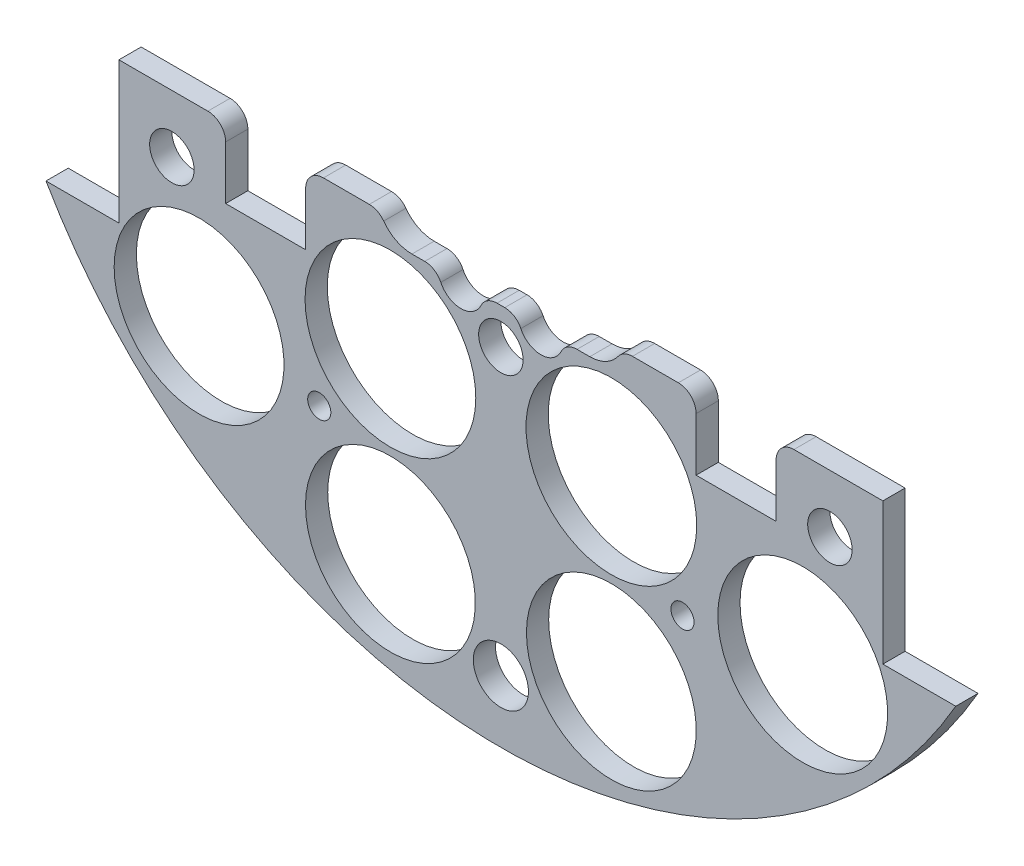
SolidWorks part; units mm, degrees
ref_plane "Front Plane" through (0, 0, 0) normal (0, 0, 1) x (1, 0, 0)
ref_plane "Top Plane" through (0, 0, 0) normal (0, 1, 0) x (1, 0, 0)
ref_plane "Right Plane" through (0, 0, 0) normal (1, 0, 0) x (0, 0, -1)
sketch "Sketch1" plane through (0, 0, 0) normal (0, 0, 1) x (1, 0, 0)
  line L0 (0, 0) -> (-82.1241, 0) construction
  line L1 (0, 0) -> (0, 95.6219) construction
  line L3 (-64.9644, 37.338) -> (-54.5504, 37.338)
  line L5 (-64.9644, -37.338) -> (-54.5504, -37.338)
  line L6 (-54.5504, 37.338) -> (-54.5504, -37.338)
  line L7 (64.9644, -37.338) -> (54.5504, -37.338)
  line L8 (64.9644, 37.338) -> (54.5504, 37.338)
  line L9 (54.5504, 37.338) -> (54.5504, -37.338)
  arc A0 (-64.9644, -37.338) -> (64.9644, -37.338) centre (0, 0) ccw
  circle A1 centre (-46.482, 11.049) radius 1.651
  circle A2 centre (-21.0833, 10.795) radius 1.651
  circle A3 centre (-21.0833, -10.795) radius 1.651
  circle A4 centre (-46.482, -11.049) radius 1.651
  circle A5 centre (46.482, -11.049) radius 1.651
  circle A6 centre (21.0833, -10.795) radius 1.651
  circle A7 centre (21.0833, 10.795) radius 1.651
  circle A8 centre (46.482, 11.049) radius 1.651
  arc A9 (64.9644, 37.338) -> (-64.9644, 37.338) centre (0, 0) ccw
  dimension "D2" = 3.302
  dimension "D3" = 3.302
  dimension "D4" = 25.4
  dimension "D5" = 10.795
  dimension "D10" = 46.482
  dimension "D6" = 74.676
  dimension "D7" = 10.414
  dimension "D8" = 74.93
  dimension "D9" = 74.93
  dimension "D11" = 37.338
extrude "Boss-Extrude2" add sketch "Sketch1" along normal blind 3.175
sketch "Sketch2" plane through (0, 0, 3.175) normal (0, 0, 1) x (1, 0, 0)
  line L0 (0, 68.58) -> (0, 55.88) construction
  line L1 (-9.525, 68.58) -> (9.525, 68.58)
  line L2 (-9.525, 68.58) -> (-9.525, 55.88)
  line L3 (-9.525, 55.88) -> (9.525, 55.88)
  line L4 (9.525, 68.58) -> (9.525, 55.88)
  line L5 (-9.525, 62.23) -> (9.525, 62.23) construction
  arc A0 (64.9644, 37.338) -> (-64.9644, 37.338) centre (0, 0) ccw construction
  circle A1 centre (-21.0833, 10.795) radius 1.651 construction
  circle A2 centre (21.0833, 10.795) radius 1.651 construction
  circle A3 centre (-6.731, 62.23) radius 1.143
  circle A4 centre (6.731, 62.23) radius 1.143
  dimension "D4" = 2.286
  dimension "D5" = 0
  dimension "D6" = 6.731
  dimension "D1" = 19.05
  dimension "D2" = 12.7
  dimension "D3" = 55.88
extrude "Cut-Extrude1" cut sketch "Sketch2" against normal through all contours A3 | A4
sketch "Sketch3" plane through (0, 0, 0) normal (0, 0, -1) x (-1, 0, 0)
  line L0 (0, 0) -> (0, -116.2908) construction
  line L1 (0, 0) -> (-153.8039, 0) construction
  line L2 (0, 0) -> (15.2681, -56.9814) construction
  line L3 (0, 0) -> (15.2302, -26.3795) construction
  circle A0 centre (-15.7776, -58.8828) radius 12.1285
  circle A3 centre (15.7776, -58.8828) radius 12.1285
  circle A4 centre (-43.1052, -43.1052) radius 12.1285
  circle A8 centre (-43.1052, 43.1052) radius 12.1285
  circle A11 centre (43.1052, 43.1052) radius 12.1285
  circle A14 centre (43.1052, -43.1052) radius 12.1285
  circle A33 centre (58.8828, -15.7776) radius 12.1285 [skipped]
  circle A34 centre (58.8828, 15.7776) radius 12.1285 [skipped]
  circle A35 centre (-58.8828, 15.7776) radius 12.1285 [skipped]
  circle A36 centre (-58.8828, -15.7776) radius 12.1285 [skipped]
  circle A37 centre (-15.7776, 58.8828) radius 12.1285 [skipped]
  circle A38 centre (15.7776, 58.8828) radius 12.1285 [skipped]
  point P36 (0, 0)
  point P53 (0, 0)
  point P55 (0, 0)
  dimension "D3" = 0
  dimension "D4" = 15
  dimension "D5" = 24.257
  dimension "D7" = 12
  dimension "D9" = 30
extrude "Cut-Extrude2" cut sketch "Sketch3" against normal through all
sketch "Sketch4" plane through (0, 0, 0) normal (0, 0, -1) x (-1, 0, 0)
  line L1 (-15.7702, 56.3138) -> (12.7925, 56.3138)
  line L2 (-15.7702, 56.3138) -> (-15.7702, 67.9913)
  line L3 (-15.7702, 67.9913) -> (12.7925, 67.9913)
  line L4 (12.7925, 56.3138) -> (12.7925, 67.9913)
extrude "Boss-Extrude3" add sketch "Sketch4" against normal up to surface (3.175 mm away) up to face at (-55.2337, -43.1052, 3.175)
sketch "Sketch5" plane through (0, 0, 0) normal (0, 0, -1) x (-1, 0, 0)
  line L1 (-85.044, -17.145) -> (131.6774, -17.145)
  line L2 (-85.044, -17.145) -> (-85.044, 113.4242)
  line L3 (-85.044, 113.4242) -> (131.6774, 113.4242)
  line L4 (131.6774, -17.145) -> (131.6774, 113.4242)
  circle A0 centre (-21.0833, -10.795) radius 1.651 construction
  dimension "D1" = 6.35
extrude "Cut-Extrude4" cut sketch "Sketch5" against normal through all contours L2 L3 L4 L1
extrude "Cut-Extrude5" cut sketch "Sketch6" against normal through all both and the other way through all
sketch "Sketch6" plane through (31.3134, 132.614, -3.175) normal (0, 0, -1) x (0, 1, 0)
  line L0 (-132.614, -31.3134) -> (-132.614, 57.8454) construction
  line L1 (-132.614, -31.3134) -> (-222.516, -31.3134) construction
  circle A0 centre (-158.014, 14.4066) radius 3.175
  circle A1 centre (-173.254, -31.3134) radius 3.175
  circle A3 centre (-158.014, -77.0334) radius 3.175
  circle A4 centre (-107.214, -77.0334) radius 3.175
  circle A5 centre (-91.974, -31.3134) radius 3.175
  circle A6 centre (-107.214, 14.4066) radius 3.175
extrude "Cut-Extrude7" cut sketch "Sketch8" against normal blind 29.21
sketch "Sketch8" plane through (31.3134, 132.559, 0) normal (0, 0, -1) x (0, 1, 0)
  line L0 (-132.559, -31.3134) -> (6.1626, -31.3134) construction
  line L2 (-132.559, -31.3134) -> (-132.559, -122.6589) construction
  circle A0 centre (-190.979, 2.9766) radius 1.651
  circle A2 centre (-154.784, -31.3134) radius 1.651
  circle A3 centre (-190.979, -65.6034) radius 1.651
  circle A4 centre (-110.334, -31.3134) radius 1.651
  circle A5 centre (-74.139, -65.6034) radius 1.651
  circle A6 centre (-74.139, 2.9766) radius 1.651
sketch "Sketch11" plane through (0, 0, 0) normal (0, 0, -1) x (-1, 0, 0)
  line L0 (-54.5504, -17.145) -> (54.5504, -17.145) construction
  circle A0 centre (0, -66.045) radius 3.937
  point P4 (0, -17.145)
  dimension "D1" = 7.874
  dimension "D2" = 48.9
extrude "Cut-Extrude11" cut sketch "Sketch11" against normal through all
sketch "Sketch12" plane through (0, 0, 0) normal (0, 0, -1) x (-1, 0, 0)
  line L0 (-54.5504, -17.145) -> (54.5504, -17.145) construction
  line L1 (-39.3104, -17.145) -> (-27.8804, -17.145)
  line L2 (-39.3104, -17.145) -> (-39.3104, -27.305)
  line L3 (-39.3104, -27.305) -> (-27.8804, -27.305)
  line L4 (-27.8804, -17.145) -> (-27.8804, -27.305)
  line L5 (-54.5504, -37.338) -> (-54.5504, -17.145) construction
  line L6 (27.8804, -17.145) -> (39.3104, -17.145)
  line L7 (27.8804, -17.145) -> (27.8804, -27.305)
  line L8 (27.8804, -27.305) -> (39.3104, -27.305)
  line L9 (39.3104, -17.145) -> (39.3104, -27.305)
  line L10 (0, -10.2409) -> (0, -88.0539) construction
  dimension "D1" = 15.24
  dimension "D2" = 11.43
  dimension "D3" = 10.16
extrude "Cut-Extrude12" cut sketch "Sketch12" against normal through all
sketch "Sketch16" plane through (0, 0, 0) normal (0, 0, -1) x (-1, 0, 0)
  line L0 (0, 0) -> (0, 27.5884) construction
  circle A0 centre (15.7776, -33.4828) radius 12.192
  circle A2 centre (15.7776, -58.8828) radius 12.1285 construction
  circle A3 centre (-15.7776, -33.4828) radius 12.192
  dimension "D1" = 24.384
  dimension "D2" = 25.4
  dimension "D3" = 0
extrude "Cut-Extrude16" cut sketch "Sketch16" against normal blind 21.59
sketch "Sketch57" plane through (0, 0, 0) normal (0, 0, -1) x (-1, 0, 0)
  line L0 (0, 0) -> (0, -110.6636) construction
  circle A0 centre (-25.9376, -45.6452) radius 1.651
  circle A1 centre (-43.1052, -43.1052) radius 12.1285 construction
  circle A2 centre (-15.7776, -33.4828) radius 12.192 construction
  circle A3 centre (25.9376, -45.6452) radius 1.651
  dimension "D1" = 3.302
  dimension "D2" = 2.54
  dimension "D3" = 10.16
extrude "Cut-Extrude57" cut sketch "Sketch57" against normal blind 58.674
extrude "Cut-Extrude58" cut sketch "Sketch58" against normal blind 48.768 and the other way blind 103.378
sketch "Sketch58" plane through (30.092, 4.0835, 36.1315) normal (0, 0, -1) x (-1, 0, 0)
  line L0 (30.092, -4.0835) -> (148.6336, -4.0835) construction
  line L1 (30.092, -4.0835) -> (30.092, 90.452) construction
  circle A0 centre (-16.898, 21.3165) radius 3.175
  circle A1 centre (77.082, 21.3165) radius 3.175
  circle A2 centre (30.092, 21.3165) radius 3.175
  circle A4 centre (77.082, -29.4835) radius 3.175
  circle A5 centre (30.092, -29.4835) radius 3.175
  circle A6 centre (-16.898, -29.4835) radius 3.175
sketch "Sketch15" plane through (0, 0, 0) normal (0, 0, -1) x (-1, 0, 0)
  line L0 (0, 0) -> (0, 42.4042) construction
  line L1 (-12.7, -20.24) -> (-8.889, -20.24)
  line L2 (-2.541, -20.24) -> (2.541, -20.24)
  line L3 (-1.06, -15.24) -> (7.7, -15.24)
  line L4 (8.889, -20.24) -> (12.7, -20.24)
  arc A0 (-9.38, -11.5013) -> (-12.7, -20.24) centre (-12.7, -15.24) ccw
  arc A1 (7.7, -15.24) -> (12.7, -20.24) centre (12.7, -15.24) cw
  arc A2 (-1.06, -15.24) -> (-9.38, -11.5013) centre (-6.06, -15.24) ccw
  arc A3 (-8.889, -20.24) -> (-2.541, -20.24) centre (-5.715, -20.32) ccw
  arc A4 (2.541, -20.24) -> (8.889, -20.24) centre (5.715, -20.32) ccw
  dimension "D1" = 10
  dimension "D4" = 6.35
  dimension "D6" = 6.35
  dimension "D2" = 15.24
  dimension "D3" = 12.7
  dimension "D5" = 6.64
  dimension "D7" = 11.43
  dimension "D8" = 5.715
  dimension "D9" = 20.32
extrude "Cut-Extrude15" cut sketch "Sketch15" against normal blind 21.59
fillet "Fillet1" radius 2.54 10 edges at (-27.8804, -17.145, 1.5875) (-39.3104, -17.145, 1.5875) (-17.3229, -17.145, 1.5875) (-8.889, -20.24, 1.5875) (-2.541, -20.24, 1.5875) (2.541, -20.24, 1.5875) (8.889, -20.24, 1.5875) (17.3229, -17.145, 1.5875) (27.8804, -17.145, 1.5875) (39.3104, -17.145, 1.5875)
